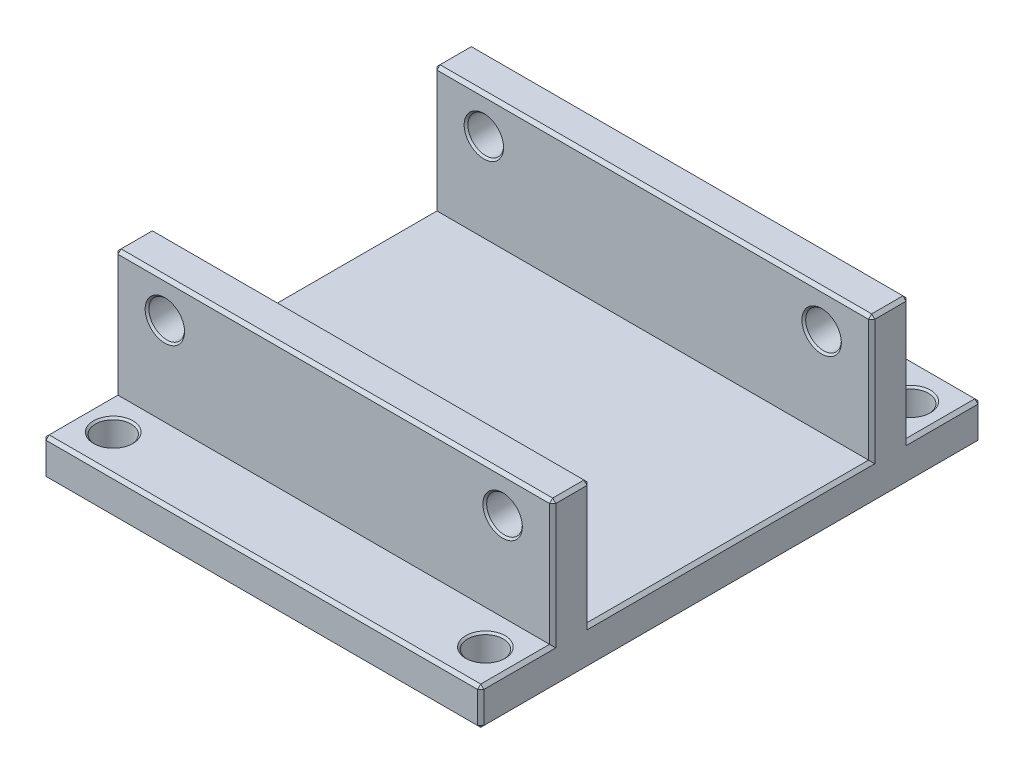
SolidWorks part; units mm, degrees
ref_plane "Front Plane" through (0, 0, 0) normal (0, 0, 1) x (1, 0, 0)
ref_plane "Top Plane" through (0, 0, 0) normal (0, 1, 0) x (1, 0, 0)
ref_plane "Right Plane" through (0, 0, 0) normal (1, 0, 0) x (0, 0, -1)
ref_plane "평면1" through (0, 26, 0) normal (0, 1, 0) x (1, 0, 0)
sketch "스케치1" plane through (0, 26, 0) normal (0, 1, 0) x (1, 0, 0)
  line L0 (35, 40) -> (-35, 40)
  line L1 (-35, 40) -> (-35, -40)
  line L2 (-35, -40) -> (35, -40)
  line L3 (35, -40) -> (35, 40)
extrude "보스-돌출1" add sketch "스케치1" against normal blind 26
sketch "스케치2" plane through (35, 0, 0) normal (1, 0, 0) x (0, 0, -1)
  line L0 (-28.5, 6) -> (-28.5, 26)
  line L1 (-28.5, 26) -> (-40, 26)
  line L2 (-40, 26) -> (-40, 6)
  line L3 (-40, 6) -> (-28.5, 6)
extrude "컷-돌출1" cut sketch "스케치2" against normal through all
sketch "스케치3" plane through (35, 0, 0) normal (1, 0, 0) x (0, 0, -1)
  line L0 (-22.5, 26) -> (-22.5, 6)
  line L1 (-22.5, 6) -> (22.5, 6)
  line L2 (22.5, 6) -> (22.5, 26)
  line L3 (22.5, 26) -> (-22.5, 26)
extrude "컷-돌출2" cut sketch "스케치3" against normal through all
sketch "스케치4" plane through (35, 0, 0) normal (1, 0, 0) x (0, 0, -1)
  line L0 (28.5, 26) -> (28.5, 6)
  line L1 (28.5, 6) -> (40, 6)
  line L2 (40, 6) -> (40, 26)
  line L3 (40, 26) -> (28.5, 26)
extrude "컷-돌출3" cut sketch "스케치4" against normal through all
hole_wizard "Ø5.7 (5.7) Diameter Hole1" positions "스케치6" profile "스케치5" hole size "Ø5.7" standard "ANSI Metric"
sketch "스케치6" plane through (0, 6, 0) normal (0, 1, 0) x (1, 0, 0)
  point P0 (-29.75, 34)
sketch "스케치5" plane through (-29.75, 6, -34) normal (1, 0, 0) x (0, 0, 1)
  line L0 (0, 0) -> (0, 6)
  line L1 (0, 6) -> (2.85, 6)
  line L2 (2.85, 6) -> (2.85, 0)
  line L5 (2.85, 0) -> (0, 0)
  line L11 (0, -6.35) -> (0, 107.95) construction
  dimension "Thru Hole Dia." = 5.7
  dimension "Thru Hole Depth" = 6
hole_wizard "Ø5.7 (5.7) Diameter Hole2" positions "스케치8" profile "스케치7" hole size "Ø5.7" standard "ANSI Metric"
sketch "스케치8" plane through (0, 0, 0) normal (0, -1, 0) x (-1, 0, 0)
  point P0 (-29.75, -34)
  point P1 (-29.75, 34)
  point P2 (29.75, -34)
sketch "스케치7" plane through (29.75, 0, 34) normal (1, 0, 0) x (0, 0, -1)
  line L0 (0, 0) -> (0, 26)
  line L1 (0, 26) -> (2.85, 26)
  line L2 (2.85, 26) -> (2.85, 0)
  line L5 (2.85, 0) -> (0, 0)
  line L11 (0, -6.35) -> (0, 107.95) construction
  dimension "Thru Hole Dia." = 5.7
  dimension "Thru Hole Depth" = 26
hole_wizard "Ø5.7 (5.7) Diameter Hole3" positions "스케치10" profile "스케치9" hole size "Ø5.7" standard "ANSI Metric"
sketch "스케치10" plane through (0, 0, -22.5) normal (0, 0, 1) x (1, 0, 0)
  point P0 (-27, 20.1)
sketch "스케치9" plane through (-27, 20.1, -22.5) normal (1, 0, 0) x (0, -1, 0)
  line L0 (0, 0) -> (0, 17.5)
  line L1 (0, 17.5) -> (2.85, 17.5)
  line L2 (2.85, 17.5) -> (2.85, 0)
  line L5 (2.85, 0) -> (0, 0)
  line L11 (0, -6.35) -> (0, 107.95) construction
  dimension "Thru Hole Dia." = 5.7
  dimension "Thru Hole Depth" = 17.5
hole_wizard "Ø5.7 (5.7) Diameter Hole4" positions "스케치12" profile "스케치11" hole size "Ø5.7" standard "ANSI Metric"
sketch "스케치12" plane through (0, 0, -28.5) normal (0, 0, -1) x (-1, 0, 0)
  point P0 (-27, 20.1)
sketch "스케치11" plane through (27, 20.1, -28.5) normal (1, 0, 0) x (0, 1, 0)
  line L0 (0, 0) -> (0, 6)
  line L1 (0, 6) -> (2.85, 6)
  line L2 (2.85, 6) -> (2.85, 0)
  line L5 (2.85, 0) -> (0, 0)
  line L11 (0, -6.35) -> (0, 107.95) construction
  dimension "Thru Hole Dia." = 5.7
  dimension "Thru Hole Depth" = 6
hole_wizard "Ø5.7 (5.7) Diameter Hole5" positions "스케치14" profile "스케치13" hole size "Ø5.7" standard "ANSI Metric"
sketch "스케치14" plane through (0, 0, 28.5) normal (0, 0, 1) x (1, 0, 0)
  point P0 (-27, 20.1)
sketch "스케치13" plane through (-27, 20.1, 28.5) normal (1, 0, 0) x (0, -1, 0)
  line L0 (0, 0) -> (0, 68.5)
  line L1 (0, 68.5) -> (2.85, 68.5)
  line L2 (2.85, 68.5) -> (2.85, 0)
  line L5 (2.85, 0) -> (0, 0)
  line L11 (0, -6.35) -> (0, 107.95) construction
  dimension "Thru Hole Dia." = 5.7
  dimension "Thru Hole Depth" = 68.5
hole_wizard "Ø5.7 (5.7) Diameter Hole6" positions "스케치16" profile "스케치15" hole size "Ø5.7" standard "ANSI Metric"
sketch "스케치16" plane through (0, 0, 22.5) normal (0, 0, -1) x (-1, 0, 0)
  point P0 (-27, 20.1)
sketch "스케치15" plane through (27, 20.1, 22.5) normal (1, 0, 0) x (0, 1, 0)
  line L0 (0, 0) -> (0, 17.5)
  line L1 (0, 17.5) -> (2.85, 17.5)
  line L2 (2.85, 17.5) -> (2.85, 0)
  line L5 (2.85, 0) -> (0, 0)
  line L11 (0, -6.35) -> (0, 107.95) construction
  dimension "Thru Hole Dia." = 5.7
  dimension "Thru Hole Depth" = 17.5
chamfer "모따기1" distance 0.3 angle 45 16 edges at (-29.75, 0, -31.15) (-24.15, 20.1, -28.5) (-24.15, 20.1, 22.5) (-29.75, 6, -31.15) (-24.15, 20.1, 28.5) (24.15, 20.1, -22.5) (29.75, 6, -36.85) (29.75, 0, -36.85) (24.15, 20.1, 28.5) (24.15, 20.1, 22.5) (-24.15, 20.1, -22.5) (24.15, 20.1, -28.5) (29.75, 6, 31.15) (-29.75, 6, 31.15) (29.75, 0, 31.15) (-29.75, 0, 31.15)
chamfer "모따기2" distance 0.5 angle 45 32 edges at (0, 0, -40) (-35, 3, -40) (35, 0, 0) (-35, 0, 0) (0, 0, 40) (0, 6, -40) (35, 3, -40) (-35, 6, -34.25) (-35, 16, -28.5) (-35, 26, -25.5) (35, 3, 40) (-35, 3, 40) (0, 6, 40) (0, 26, -28.5) (35, 6, -34.25) (35, 16, -28.5) (35, 6, 34.25) (35, 16, 28.5) (-35, 6, 34.25) (-35, 16, 28.5) (0, 26, 28.5) (0, 26, -22.5) (35, 26, -25.5) (-35, 16, -22.5) (-35, 6, 0) (-35, 16, 22.5) (35, 26, 25.5) (-35, 26, 25.5) (35, 16, -22.5) (35, 6, 0) (35, 16, 22.5) (0, 26, 22.5)
